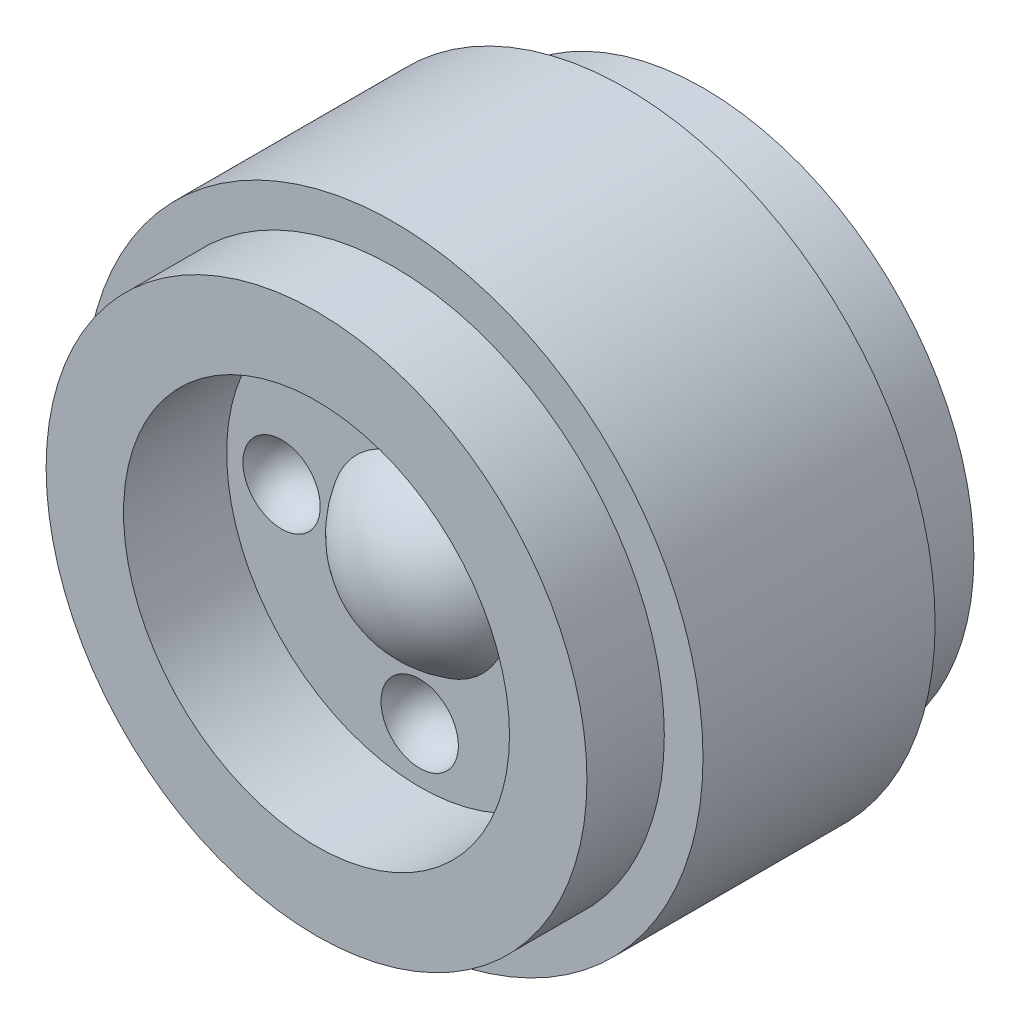
SolidWorks part; units mm, degrees
material "AISI 1035 Steel (SS)"
ref_plane "Front Plane" through (0, 0, 0) normal (0, 0, 1) x (1, 0, 0)
ref_plane "Top Plane" through (0, 0, 0) normal (0, 1, 0) x (1, 0, 0)
ref_plane "Right Plane" through (0, 0, 0) normal (1, 0, 0) x (0, 0, -1)
sketch "Sketch1" plane through (0, 0, 0) normal (1, 0, 0) x (0, 0, -1)
  line L0 (-4.4348, 0) -> (1.6154, 0)
  line L1 (6.0503, 3.2258) -> (6.0503, 8.4557)
  line L2 (6.0503, 3.2258) -> (1.6154, 3.2258)
  line L3 (1.6154, 3.2258) -> (1.6154, 0)
  line L4 (3.6297, 9.6647) -> (-3.6297, 9.6647)
  line L5 (3.6297, 9.6647) -> (3.6297, 8.4557)
  line L6 (6.0503, 8.4557) -> (3.6297, 8.4557)
  line L7 (-3.6297, 9.6647) -> (-3.6297, 8.4557)
  line L8 (-3.6297, 8.4557) -> (-6.0503, 8.4557)
  line L10 (-6.0503, 8.4557) -> (-6.0503, 6.035)
  line L11 (-6.0503, 6.035) -> (-2.8245, 6.035)
  line L12 (-2.8245, 6.035) -> (-2.8245, 2.7922)
  arc A0 (-2.8245, 2.7922) -> (-4.4348, 0) centre (-1.209, 0) ccw
revolve "Revolve1" add sketch "Sketch1" angle 360 about L0
sketch "Sketch2" plane through (0, 0, 2.8245) normal (0, 0, 1) x (1, 0, 0)
  line L0 (-1.209, 4.318) -> (1.209, 4.318)
  arc A0 (1.209, 4.318) -> (-1.209, 4.318) centre (0, 4.318) ccw
  circle A1 centre (0, 0) radius 2.7922 construction
  dimension "D1" = 4.318
  dimension "D2" = 2.4181
revolve "Cut-Revolve1" cut sketch "Sketch2" angle 360 about L0
pattern_circular "CirPattern1" count 4 every 90 about axis through (0, 0, 0) along (0, 0, 1) of "Cut-Revolve1"
